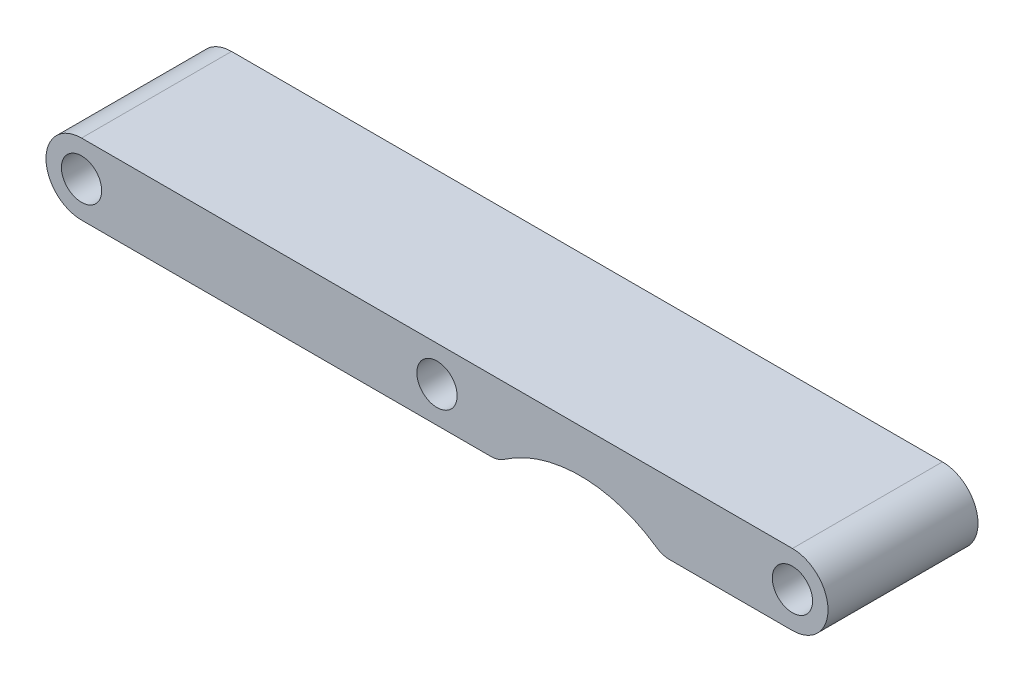
SolidWorks part; units mm, degrees
ref_plane "Front Plane" through (0, 0, 0) normal (0, 0, 1) x (1, 0, 0)
ref_plane "Top Plane" through (0, 0, 0) normal (0, 1, 0) x (1, 0, 0)
ref_plane "Right Plane" through (0, 0, 0) normal (1, 0, 0) x (0, 0, -1)
sketch "Sketch1" plane through (0, 0, 0) normal (0, 0, 1) x (1, 0, 0)
  line L0 (38.1, 7.62) -> (38.1, 0) construction
  line L1 (0, 7.62) -> (76.2, 7.62)
  line L2 (0, 7.62) -> (0, 0) construction
  line L3 (0, 0) -> (76.2, 0) construction
  line L4 (76.2, 7.62) -> (76.2, 0) construction
  line L5 (62.2194, 0) -> (76.2, 0)
  line L6 (0, 0) -> (44.7016, 0)
  line L7 (53.4605, 3.81) -> (53.4605, -11.2878) construction
  line L8 (0, 3.81) -> (76.2, 3.81) construction
  arc A0 (76.2, 7.62) -> (76.2, 0) centre (76.2, 3.81) cw
  arc A1 (0, 7.62) -> (0, 0) centre (0, 3.81) ccw
  circle A2 centre (0, 3.81) radius 2.159
  circle A3 centre (38.1, 3.81) radius 2.159
  circle A4 centre (76.2, 3.81) radius 2.159
  arc A5 (44.7016, 0) -> (62.2194, 0) centre (53.4605, -11.2878) cw
  dimension "D3" = 4.318
  dimension "D4" = 14.2875
  dimension "D5" = 22.7395
  dimension "D1" = 76.2
  dimension "D2" = 7.62
  dimension "D6" = 15.0978
extrude "Boss-Extrude1" add sketch "Sketch1" along normal blind 16.0782
fillet "Fillet1" radius 2.54 2 edges at (62.2194, 0, 8.0391) (44.7016, 0, 8.0391)
